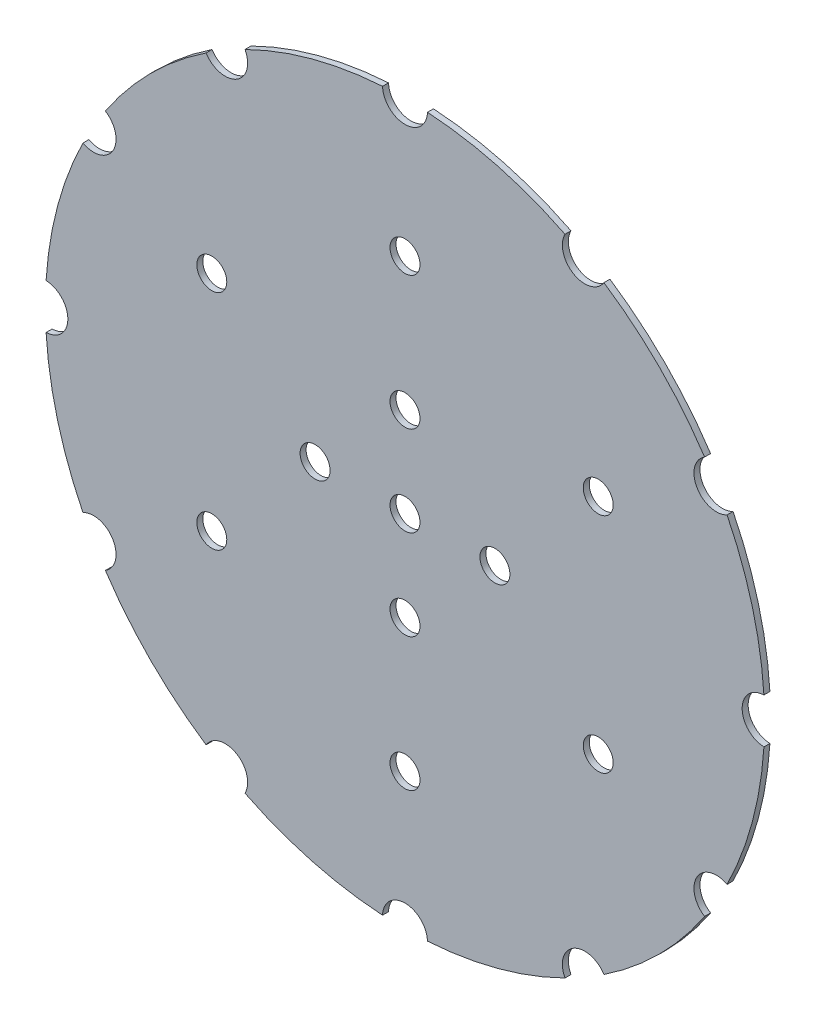
SolidWorks part; units mm, degrees
ref_plane "Front Plane" through (0, 0, 0) normal (0, 0, 1) x (1, 0, 0)
ref_plane "Top Plane" through (0, 0, 0) normal (0, 1, 0) x (1, 0, 0)
ref_plane "Right Plane" through (0, 0, 0) normal (1, 0, 0) x (0, 0, -1)
sketch "Sketch1" plane through (0, 0, 0) normal (0, 0, 1) x (1, 0, 0)
  circle A0 centre (0, 0) radius 152.4
  dimension "D1" = 304.8
extrude "Boss-Extrude1" add sketch "Sketch1" along normal blind 2.54
sketch "Sketch2" plane through (0, 0, 0) normal (0, 0, 1) x (1, 0, 0)
  line L0 (152.4, 0) -> (-152.4, 0) construction
  line L1 (131.9823, -76.2) -> (0, 0) construction
  circle A2 centre (152.4, 0) radius 9.525
  circle A3 centre (0, 0) radius 152.4 construction
  circle A4 centre (131.9823, -76.2) radius 9.525
  circle A5 centre (76.2, -131.9823) radius 9.525
  circle A6 centre (0, -152.4) radius 9.525
  circle A7 centre (-76.2, -131.9823) radius 9.525
  circle A8 centre (-131.9823, -76.2) radius 9.525
  circle A9 centre (-152.4, 0) radius 9.525
  circle A10 centre (-131.9823, 76.2) radius 9.525
  circle A11 centre (-76.2, 131.9823) radius 9.525
  circle A12 centre (0, 152.4) radius 9.525
  circle A13 centre (76.2, 131.9823) radius 9.525
  circle A14 centre (131.9823, 76.2) radius 9.525
  circle A15 centre (38.1, 0) radius 6.35
  circle A17 centre (0, -38.1) radius 6.35
  circle A18 centre (-38.1, 0) radius 6.35
  circle A19 centre (0, 38.1) radius 6.35
  circle A20 centre (81.8793, -47.273) radius 6.35
  circle A21 centre (0, -94.546) radius 6.35
  circle A22 centre (-81.8793, -47.273) radius 6.35
  circle A23 centre (-81.8793, 47.273) radius 6.35
  circle A24 centre (0, 94.546) radius 6.35
  circle A25 centre (81.8793, 47.273) radius 6.35
  point P9 (143.5591, -3.4073)
  point P31 (0, 0)
  point P40 (0, 0)
  point P55 (0, 0)
  dimension "D1" = 19.05
  dimension "D3" = 12.7
  dimension "D6" = 6
  dimension "D2" = 12
  dimension "D4" = 38.1
  dimension "D5" = 4
extrude "Cut-Extrude2" cut sketch "Sketch2" along normal through all
sketch "Sketch4" plane through (0, 0, 0) normal (0, 0, 1) x (1, 0, 0)
  circle A0 centre (0, 0) radius 6.35
  dimension "D1" = 12.7
extrude "Cut-Extrude4" cut sketch "Sketch4" along normal blind 2.54
